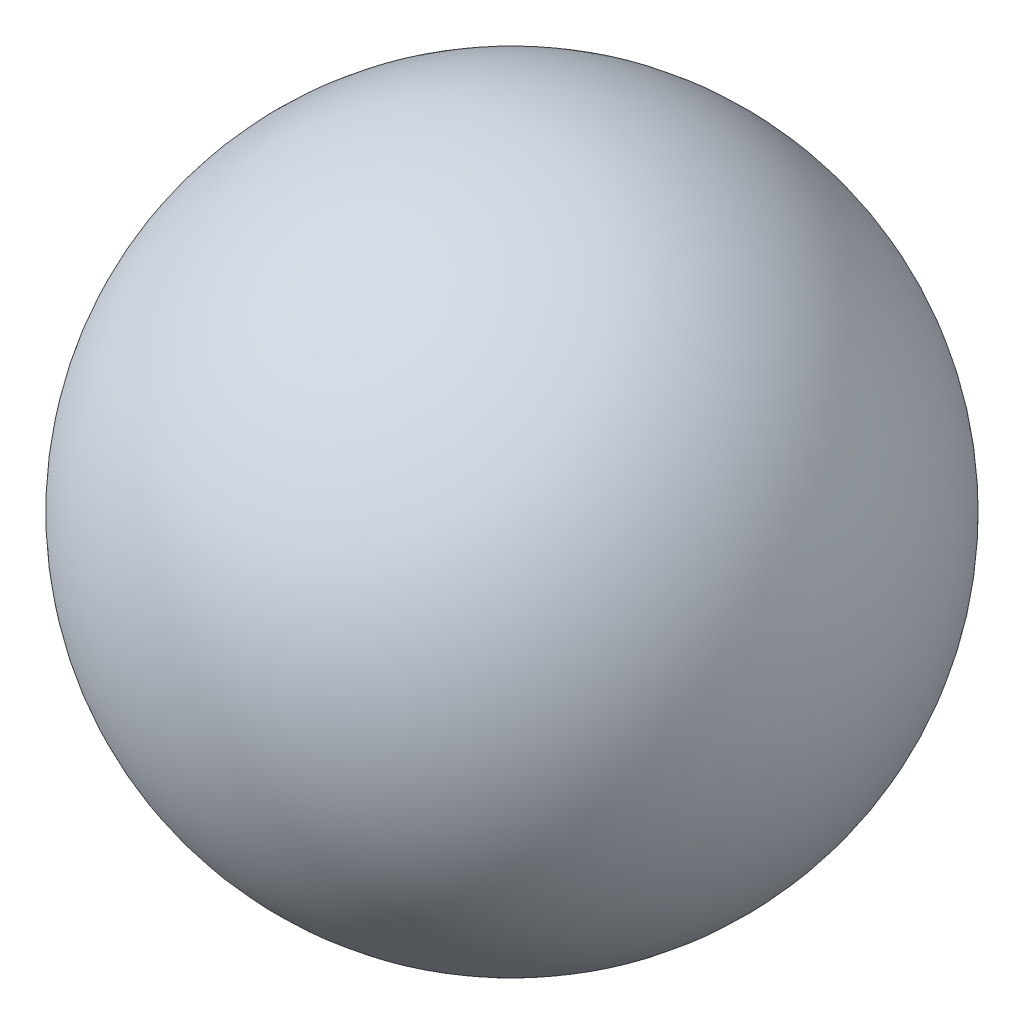
SolidWorks part; units mm, degrees
ref_plane "Front Plane" through (0, 0, 0) normal (0, 0, 1) x (1, 0, 0)
ref_plane "Top Plane" through (0, 0, 0) normal (0, 1, 0) x (1, 0, 0)
ref_plane "Right Plane" through (0, 0, 0) normal (1, 0, 0) x (0, 0, -1)
sketch "Sketch1" plane through (0, 0, 0) normal (0, 0, 1) x (1, 0, 0)
  line L0 (0, 0) -> (0, 78.6831) construction
  line L1 (0, 67.9894) -> (0, 10.6937)
  arc A0 (0, 10.6937) -> (0, 67.9894) centre (0, 39.3415) ccw
revolve "Revolve1" add sketch "Sketch1" angle 360 about L0
